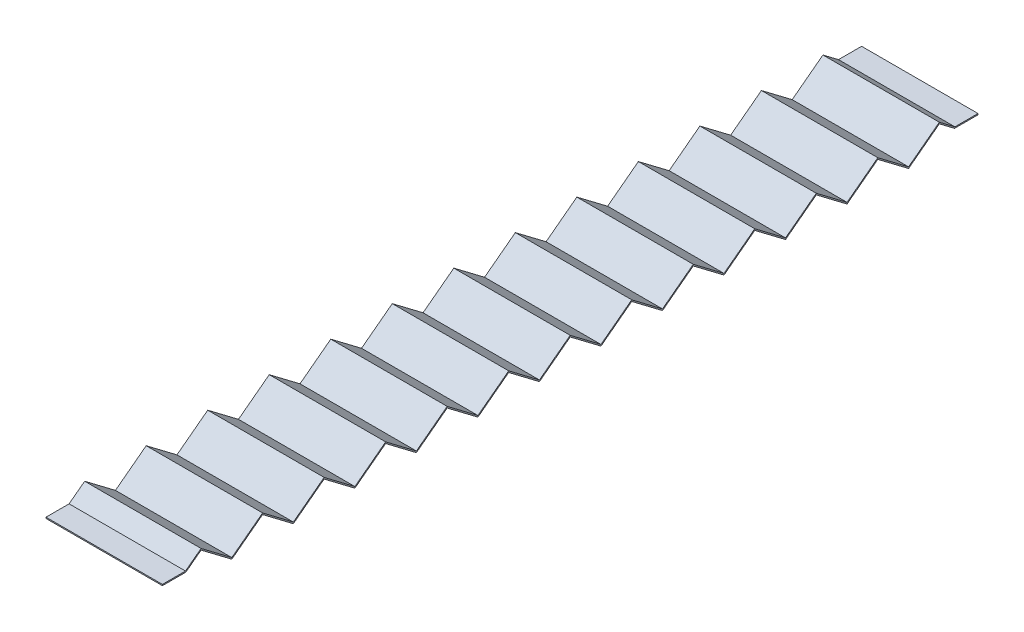
SolidWorks part; units mm, degrees
ref_plane "Front Plane" through (0, 0, 0) normal (0, 0, 1) x (1, 0, 0)
ref_plane "Top Plane" through (0, 0, 0) normal (0, 1, 0) x (1, 0, 0)
ref_plane "Right Plane" through (0, 0, 0) normal (1, 0, 0) x (0, 0, -1)
sketch "Sketch2" plane through (0, 0, 0) normal (0, 0, 1) x (1, 0, 0)
  line L1 (-27.5, 10) -> (27.5, 10)
  line L2 (-27.5, 10) -> (-27.5, 0)
  line L3 (-27.5, 0) -> (27.5, 0)
  line L4 (27.5, 10) -> (27.5, 0)
  point P4 (0, 0)
  dimension "D1" = 10
  dimension "D2" = 55
sketch "Sketch3" plane through (0, 0, 0) normal (1, 0, 0) x (0, 0, -1)
  line L0 (0, 10) -> (350.3164, 10) construction
  line L1 (0, 0) -> (350.3164, 0) construction
  line L3 (10, 5) -> (16.6063, 10)
  line L4 (16.6063, 10) -> (29.819, 0)
  line L5 (29.819, 0) -> (43.0316, 10)
  line L6 (43.0316, 10) -> (56.2443, 0)
  line L7 (56.2443, 0) -> (69.457, 10)
  line L8 (69.457, 10) -> (82.6696, 0)
  line L9 (82.6696, 0) -> (95.8823, 10)
  line L10 (95.8823, 10) -> (109.0949, 0)
  line L11 (109.0949, 0) -> (122.3076, 10)
  line L12 (122.3076, 10) -> (135.5202, 0)
  line L13 (135.5202, 0) -> (148.7329, 10)
  line L14 (148.7329, 10) -> (161.9456, 0)
  line L15 (161.9456, 0) -> (175.1582, 10)
  line L16 (175.1582, 10) -> (188.3709, 0)
  line L17 (188.3709, 0) -> (201.5835, 10)
  line L18 (201.5835, 10) -> (214.7962, 0)
  line L19 (0, 10) -> (0, 0) construction
  line L20 (214.7962, 0) -> (228.0088, 10)
  line L21 (228.0088, 10) -> (241.2215, 0)
  line L22 (241.2215, 0) -> (254.4342, 10)
  line L23 (254.4342, 10) -> (267.6468, 0)
  line L24 (267.6468, 0) -> (280.8595, 10)
  line L25 (280.8595, 10) -> (294.0721, 0)
  line L26 (294.0721, 0) -> (307.2848, 10)
  line L27 (307.2848, 10) -> (320.4974, 0)
  line L28 (320.4974, 0) -> (333.7101, 10)
  line L29 (333.7101, 10) -> (340.3164, 5)
  line L30 (350.3164, 10) -> (350.3164, 0) construction
  line L31 (10, 5) -> (0, 5)
  line L32 (340.3164, 5) -> (350.3164, 5)
  line L34 (350.3164, 22.75) -> (350.3164, 4.75) construction
  dimension "D2" = 10
  dimension "D1" = 10
  dimension "D3" = 10
extrude "Extrude-Thin1" add sketch "Sketch3" against normal mid plane 50 thin thin type mid plane wall 0.5
